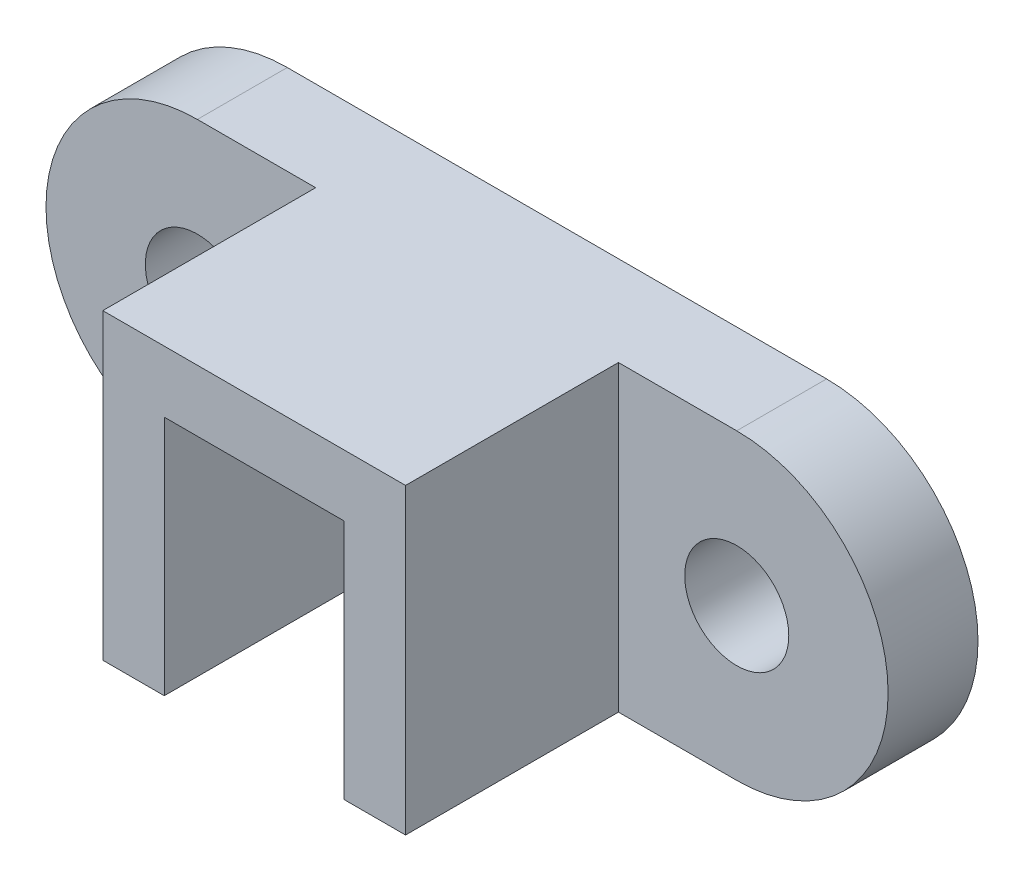
SolidWorks part; units mm, degrees
ref_plane "Front Plane" through (0, 0, 0) normal (0, 0, 1) x (1, 0, 0)
ref_plane "Top Plane" through (0, 0, 0) normal (0, 1, 0) x (1, 0, 0)
ref_plane "Right Plane" through (0, 0, 0) normal (1, 0, 0) x (0, 0, -1)
sketch "Sketch1" plane through (0, 0, 0) normal (0, 0, 1) x (1, 0, 0)
  line L0 (0, 32) -> (0, -32) construction
  line L1 (114, 32) -> (114, -32) construction
  line L3 (0, -32) -> (114, -32)
  line L4 (0, -32) -> (0, 32)
  line L5 (0, 32) -> (114, 32)
  line L6 (114, -32) -> (114, 32)
  circle A0 centre (0, 0) radius 11
  circle A1 centre (114, 0) radius 11
  arc A2 (114, 32) -> (114, -32) centre (114, 0) cw
  arc A3 (0, -32) -> (0, 32) centre (0, 0) cw
  point P4 (0, 0)
  dimension "D2" = 22
  dimension "D3" = 22
  dimension "D4" = 32
  dimension "D5" = 32
  dimension "D1" = 114
extrude "Boss-Extrude1" add sketch "Sketch1" along normal blind 19 contours A3 L4 A0 | A1 L6 L5 L4 A0 L3 | A2 L6 A1
sketch "Sketch3" plane through (0, 0, 19) normal (0, 0, 1) x (1, 0, 0)
  line L0 (57, 32) -> (57, -32) construction
  line L1 (0, 32) -> (114, 32) construction
  line L2 (0, -32) -> (114, -32) construction
  line L3 (25, 32) -> (89, 32)
  line L4 (89, 32) -> (89, -32)
  line L5 (89, -32) -> (25, -32)
  line L6 (25, -32) -> (25, 32)
  point P8 (57, 32)
  dimension "D1" = 64
extrude "Boss-Extrude2" add sketch "Sketch3" along normal blind 45
sketch "Sketch5" plane through (0, 0, 64) normal (0, 0, 1) x (1, 0, 0)
  line L0 (57, 32) -> (57, -32) construction
  line L1 (89, 32) -> (25, 32) construction
  line L2 (25, -32) -> (89, -32) construction
  line L4 (38, 19) -> (76, 19)
  line L8 (38, 19) -> (38, -32)
  line L9 (38, -32) -> (57, -32)
  line L10 (57, -32) -> (76, -32)
  line L11 (76, -32) -> (76, 19)
  point P6 (57, 0)
  dimension "D2" = 13
  dimension "D5" = 13
extrude "Cut-Extrude9" cut sketch "Sketch5" against normal blind 45
sketch "Sketch6" plane through (0, -32, 0) normal (0, -1, 0) x (1, 0, 0)
  line L0 (38, 19) -> (38, 13)
  line L1 (76, 19) -> (76, 13)
  line L2 (76, 13) -> (38, 13)
  line L3 (38, 19) -> (76, 19)
  dimension "D1" = 13
extrude "Cut-Extrude10" cut sketch "Sketch6" against normal up to surface (51 mm away) up to face at (57, 19, 41.5)
sketch "Sketch7" plane through (38, 0, 0) normal (1, 0, 0) x (0, 0, -1)
  line L0 (-64, 19) -> (-13, -32)
  line L1 (-13, -32) -> (-13, 19)
  line L2 (-13, 19) -> (-64, 19)
extrude "Boss-Extrude3" add sketch "Sketch7" along normal up to surface (38 mm away) up to face at (76, -6.5, 38.5)
